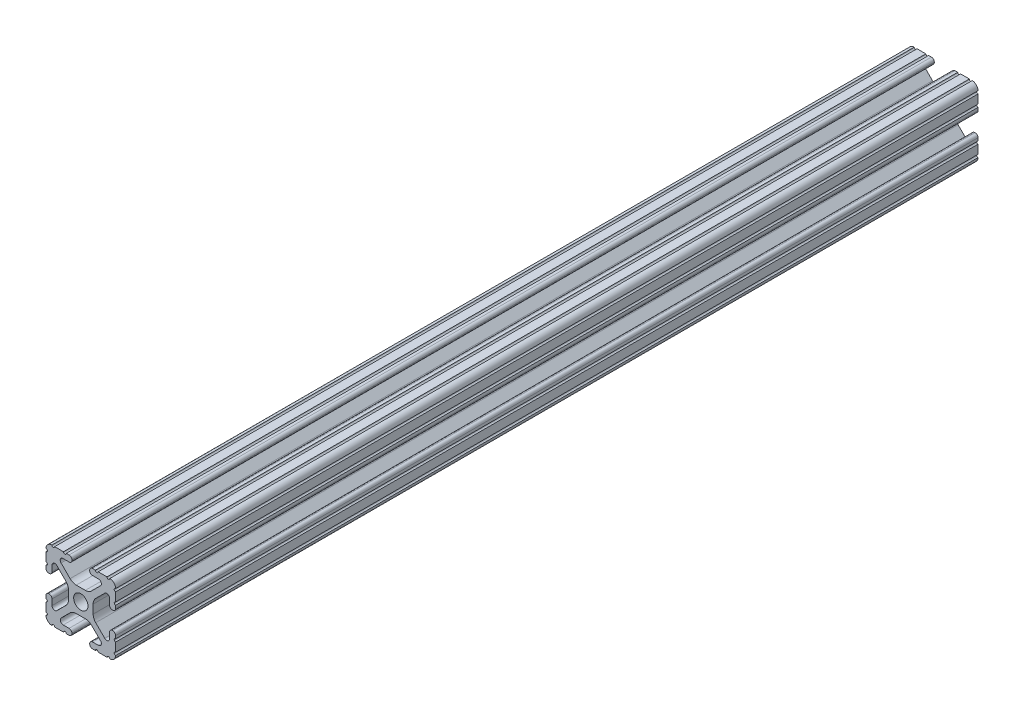
SolidWorks part; units mm, degrees
ref_plane "Front Plane" through (0, 0, 0) normal (0, 0, 1) x (1, 0, 0)
ref_plane "Top Plane" through (0, 0, 0) normal (0, 1, 0) x (1, 0, 0)
ref_plane "Right Plane" through (0, 0, 0) normal (1, 0, 0) x (0, 0, -1)
sketch "Sketch1" plane through (0, 0, 0) normal (0, 0, 1) x (1, 0, 0)
  line L88 (-7.1797, -8.6452) -> (-3.9523, -5.4237)
  line L89 (-1.7093, -4.4958) -> (1.7093, -4.4958)
  line L90 (3.9523, -5.4237) -> (7.1797, -8.6452)
  line L91 (6.4164, -10.4902) -> (4.2875, -10.4902)
  line L92 (3.2385, -11.5392) -> (3.2385, -11.651)
  line L93 (4.2875, -12.7) -> (5.3171, -12.7)
  line L94 (6.3331, -12.7) -> (9.5504, -12.7)
  line L95 (12.7, -9.5504) -> (12.7, -6.3331)
  line L96 (12.7, -5.3171) -> (12.7, -4.2875)
  line L97 (11.651, -3.2385) -> (11.5392, -3.2385)
  line L98 (10.4902, -4.2875) -> (10.4902, -6.4021)
  line L99 (8.7371, -7.1294) -> (5.441, -3.8408)
  line L100 (4.5085, -1.5932) -> (4.5085, 1.5932)
  line L101 (5.441, 3.8408) -> (8.7371, 7.1294)
  line L102 (10.4902, 6.4021) -> (10.4902, 4.2875)
  line L103 (11.5392, 3.2385) -> (11.651, 3.2385)
  line L104 (12.7, 4.2875) -> (12.7, 5.3171)
  line L105 (12.7, 6.3331) -> (12.7, 9.5504)
  line L106 (9.5504, 12.7) -> (6.3331, 12.7)
  line L107 (5.3171, 12.7) -> (4.2875, 12.7)
  line L108 (3.2385, 11.651) -> (3.2385, 11.5392)
  line L109 (4.2875, 10.4902) -> (6.4768, 10.4902)
  line L110 (7.207, 8.7244) -> (3.8983, 5.4232)
  line L111 (1.6558, 4.4958) -> (-1.6558, 4.4958)
  line L112 (-3.8983, 5.4232) -> (-7.207, 8.7244)
  line L113 (-6.4768, 10.4902) -> (-4.2875, 10.4902)
  line L114 (-3.2385, 11.5392) -> (-3.2385, 11.651)
  line L115 (-4.2875, 12.7) -> (-5.3171, 12.7)
  line L116 (-6.3331, 12.7) -> (-9.5504, 12.7)
  line L117 (-12.7, 9.5504) -> (-12.7, 6.3331)
  line L118 (-12.7, 5.3171) -> (-12.7, 4.2875)
  line L119 (-11.651, 3.2385) -> (-11.5392, 3.2385)
  line L120 (-10.4902, 4.2875) -> (-10.4902, 6.4021)
  line L121 (-8.7371, 7.1294) -> (-5.441, 3.8408)
  line L122 (-4.5085, 1.5932) -> (-4.5085, -1.5932)
  line L123 (-5.441, -3.8408) -> (-8.7371, -7.1294)
  line L124 (-10.4902, -6.4021) -> (-10.4902, -4.2875)
  line L125 (-11.5392, -3.2385) -> (-11.651, -3.2385)
  line L126 (-12.7, -4.2875) -> (-12.7, -5.3171)
  line L127 (-12.7, -6.3331) -> (-12.7, -9.5504)
  line L128 (-9.5504, -12.7) -> (-6.3331, -12.7)
  line L129 (-5.3171, -12.7) -> (-4.2875, -12.7)
  line L130 (-3.2385, -11.651) -> (-3.2385, -11.5392)
  line L131 (-4.2875, -10.4902) -> (-6.4164, -10.4902)
  circle A1 centre (0, 0) radius 2.6035
  arc A104 (-7.1797, -8.6452) -> (-6.4164, -10.4902) centre (-6.4164, -9.4098) ccw
  arc A105 (-1.7093, -4.4958) -> (-3.9523, -5.4237) centre (-1.7093, -7.6708) ccw
  arc A106 (3.9523, -5.4237) -> (1.7093, -4.4958) centre (1.7093, -7.6708) ccw
  arc A107 (6.4164, -10.4902) -> (7.1797, -8.6452) centre (6.4164, -9.4098) ccw
  arc A108 (4.2875, -10.4902) -> (3.2385, -11.5392) centre (4.2875, -11.5392) ccw
  arc A109 (3.2385, -11.651) -> (4.2875, -12.7) centre (4.2875, -11.651) ccw
  arc A110 (6.3331, -12.7) -> (5.3171, -12.7) centre (5.8251, -12.7) ccw
  arc A111 (10.5664, -12.6998) -> (9.5504, -12.7) centre (10.0584, -12.7) ccw
  arc A112 (10.5664, -12.6998) -> (12.6998, -10.5664) centre (10.5918, -10.5918) ccw
  arc A113 (12.7, -9.5504) -> (12.6998, -10.5664) centre (12.7, -10.0584) ccw
  arc A114 (12.7, -5.3171) -> (12.7, -6.3331) centre (12.7, -5.8251) ccw
  arc A115 (12.7, -4.2875) -> (11.651, -3.2385) centre (11.651, -4.2875) ccw
  arc A116 (11.5392, -3.2385) -> (10.4902, -4.2875) centre (11.5392, -4.2875) ccw
  arc A117 (8.7371, -7.1294) -> (10.4902, -6.4021) centre (9.4628, -6.4021) ccw
  arc A118 (4.5085, -1.5932) -> (5.441, -3.8408) centre (7.6835, -1.5932) ccw
  arc A119 (5.441, 3.8408) -> (4.5085, 1.5932) centre (7.6835, 1.5932) ccw
  arc A120 (10.4902, 6.4021) -> (8.7371, 7.1294) centre (9.4628, 6.4021) ccw
  arc A121 (10.4902, 4.2875) -> (11.5392, 3.2385) centre (11.5392, 4.2875) ccw
  arc A122 (11.651, 3.2385) -> (12.7, 4.2875) centre (11.651, 4.2875) ccw
  arc A123 (12.7, 6.3331) -> (12.7, 5.3171) centre (12.7, 5.8251) ccw
  arc A124 (12.6998, 10.5664) -> (12.7, 9.5504) centre (12.7, 10.0584) ccw
  arc A125 (12.6998, 10.5664) -> (10.5664, 12.6998) centre (10.5918, 10.5918) ccw
  arc A126 (9.5504, 12.7) -> (10.5664, 12.6998) centre (10.0584, 12.7) ccw
  arc A127 (5.3171, 12.7) -> (6.3331, 12.7) centre (5.8251, 12.7) ccw
  arc A128 (4.2875, 12.7) -> (3.2385, 11.651) centre (4.2875, 11.651) ccw
  arc A129 (3.2385, 11.5392) -> (4.2875, 10.4902) centre (4.2875, 11.5392) ccw
  arc A130 (7.207, 8.7244) -> (6.4768, 10.4902) centre (6.4768, 9.4563) ccw
  arc A131 (1.6558, 4.4958) -> (3.8983, 5.4232) centre (1.6558, 7.6708) ccw
  arc A132 (-3.8983, 5.4232) -> (-1.6558, 4.4958) centre (-1.6558, 7.6708) ccw
  arc A133 (-6.4768, 10.4902) -> (-7.207, 8.7244) centre (-6.4768, 9.4563) ccw
  arc A134 (-4.2875, 10.4902) -> (-3.2385, 11.5392) centre (-4.2875, 11.5392) ccw
  arc A135 (-3.2385, 11.651) -> (-4.2875, 12.7) centre (-4.2875, 11.651) ccw
  arc A136 (-6.3331, 12.7) -> (-5.3171, 12.7) centre (-5.8251, 12.7) ccw
  arc A137 (-10.5664, 12.6998) -> (-9.5504, 12.7) centre (-10.0584, 12.7) ccw
  arc A138 (-10.5664, 12.6998) -> (-12.6998, 10.5664) centre (-10.5918, 10.5918) ccw
  arc A139 (-12.7, 9.5504) -> (-12.6998, 10.5664) centre (-12.7, 10.0584) ccw
  arc A140 (-12.7, 5.3171) -> (-12.7, 6.3331) centre (-12.7, 5.8251) ccw
  arc A141 (-12.7, 4.2875) -> (-11.651, 3.2385) centre (-11.651, 4.2875) ccw
  arc A142 (-11.5392, 3.2385) -> (-10.4902, 4.2875) centre (-11.5392, 4.2875) ccw
  arc A143 (-8.7371, 7.1294) -> (-10.4902, 6.4021) centre (-9.4628, 6.4021) ccw
  arc A144 (-4.5085, 1.5932) -> (-5.441, 3.8408) centre (-7.6835, 1.5932) ccw
  arc A145 (-5.441, -3.8408) -> (-4.5085, -1.5932) centre (-7.6835, -1.5932) ccw
  arc A146 (-10.4902, -6.4021) -> (-8.7371, -7.1294) centre (-9.4628, -6.4021) ccw
  arc A147 (-10.4902, -4.2875) -> (-11.5392, -3.2385) centre (-11.5392, -4.2875) ccw
  arc A148 (-11.651, -3.2385) -> (-12.7, -4.2875) centre (-11.651, -4.2875) ccw
  arc A149 (-12.7, -6.3331) -> (-12.7, -5.3171) centre (-12.7, -5.8251) ccw
  arc A150 (-12.6998, -10.5664) -> (-12.7, -9.5504) centre (-12.7, -10.0584) ccw
  arc A151 (-12.6998, -10.5664) -> (-10.5664, -12.6998) centre (-10.5918, -10.5918) ccw
  arc A152 (-9.5504, -12.7) -> (-10.5664, -12.6998) centre (-10.0584, -12.7) ccw
  arc A153 (-5.3171, -12.7) -> (-6.3331, -12.7) centre (-5.8251, -12.7) ccw
  arc A154 (-4.2875, -12.7) -> (-3.2385, -11.651) centre (-4.2875, -11.651) ccw
  arc A155 (-3.2385, -11.5392) -> (-4.2875, -10.4902) centre (-4.2875, -11.5392) ccw
extrude "Boss-Extrude1" add sketch "Sketch1" along normal mid plane 609.6
sketch "Sketch2" plane through (0, 0, 304.8) normal (0, 0, 1) x (1, 0, 0)
  line L1 (-23.6788, 23.3515) -> (30.8552, 23.3515)
  line L2 (-23.6788, 23.3515) -> (-23.6788, -28.9582)
  line L3 (-23.6788, -28.9582) -> (30.8552, -28.9582)
  line L4 (30.8552, 23.3515) -> (30.8552, -28.9582)
extrude "Cut-Extrude1" cut sketch "Sketch2" against normal blind 294.894
